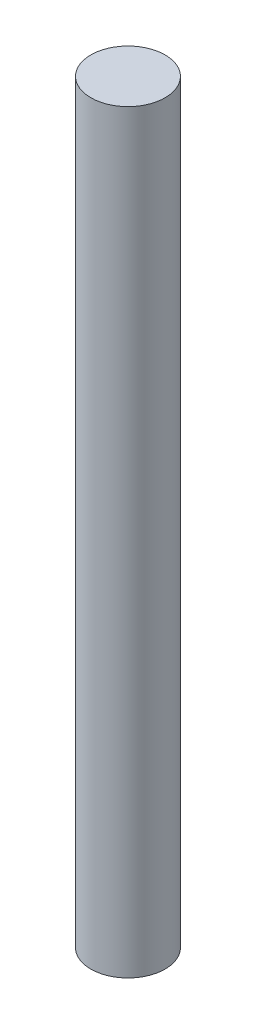
SolidWorks part; units mm, degrees
ref_plane "Front" through (0, 0, 0) normal (0, 0, 1) x (1, 0, 0)
ref_plane "Top" through (0, 0, 0) normal (0, 1, 0) x (1, 0, 0)
ref_plane "Right" through (0, 0, 0) normal (1, 0, 0) x (0, 0, -1)
sketch "Sketch1" plane through (0, 0, 0) normal (0, 1, 0) x (1, 0, 0)
  circle A0 centre (0, 0) radius 2.5
  dimension "D1" = 5
extrude "Boss-Extrude1" add sketch "Sketch1" along normal blind 50.8
